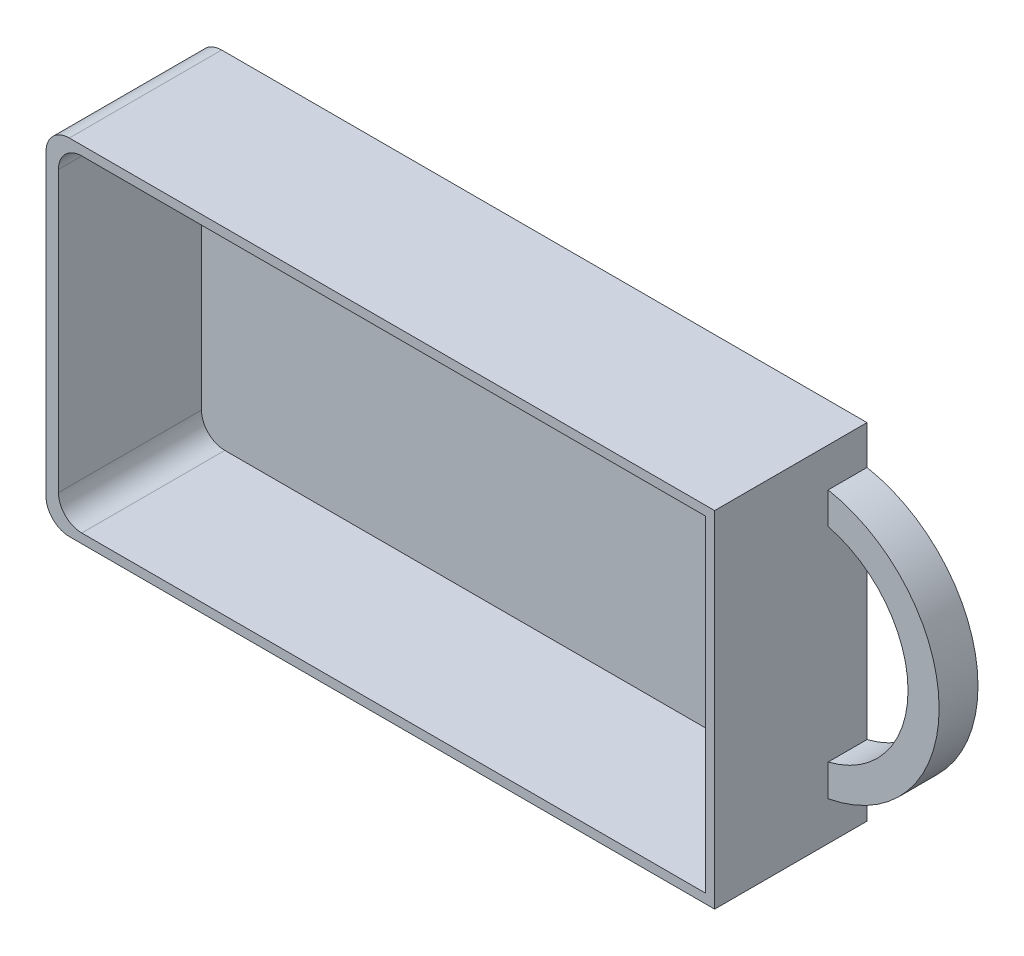
SolidWorks part; units mm, degrees
ref_plane "Спереди" through (0, 0, 0) normal (0, 0, 1) x (1, 0, 0)
ref_plane "Сверху" through (0, 0, 0) normal (0, 1, 0) x (1, 0, 0)
ref_plane "Справа" through (0, 0, 0) normal (1, 0, 0) x (0, 0, -1)
other "Configuration Table"
sketch "Эскиз1" plane through (0, 0, 0) normal (0, 0, 1) x (1, 0, 0)
  line L1 (-43, 22.2) -> (43, 22.2)
  line L2 (-43, 22.2) -> (-43, -22.2)
  line L3 (-43, -22.2) -> (43, -22.2)
  line L4 (43, 22.2) -> (43, -22.2)
  line L5 (-43, 22.2) -> (43, -22.2) construction
  line L6 (-43, -22.2) -> (43, 22.2) construction
  point P0 (0, 0)
  dimension "D1" = 86
  dimension "D2" = 44.4
extrude "Бобышка-Вытянуть1" add sketch "Эскиз1" along normal blind 19.6
sketch "Эскиз2" plane through (0, 0, 0) normal (0, 0, 1) x (1, 0, 0)
  line L0 (0, 0) -> (43, 0) construction
  line L1 (43, -22.2) -> (43, 22.2) construction
  line L2 (43, 17.2) -> (43, 13.1088)
  line L3 (43, -17.2) -> (43, -13.1088)
  arc A0 (43, -17.2) -> (43, 17.2) centre (39.7735, 0) ccw
  arc A1 (43, -13.1088) -> (43, 13.1088) centre (39.7735, 0) ccw
  dimension "D3" = 13.5
  dimension "D4" = 4
  dimension "D1" = 5
  dimension "D2" = 5
extrude "Бобышка-Вытянуть2" add sketch "Эскиз2" along normal blind 5
sketch "Эскиз3" plane through (0, 0, 19.6) normal (0, 0, 1) x (1, 0, 0)
  line L5 (-41.4, 22.2) -> (-41.4, -22.2)
  line L6 (-43, -21) -> (41.8, -21)
  line L7 (41.8, -21) -> (41.8, 21)
  line L8 (41.8, 21) -> (-43, 21)
  line L9 (-41.4, -21) -> (41.8, -21)
  line L10 (41.8, -21) -> (41.8, 21)
  line L11 (41.8, 21) -> (-41.4, 21)
  line L12 (-41.4, 21) -> (-41.4, -21)
  dimension "D1" = 1.2
  dimension "D2" = 1.6
extrude "Вырез-Вытянуть1" cut sketch "Эскиз3" against normal offset from surface (18.4 mm away) 1.2 up to face at (48.1368, 0, 0)
fillet "Скругление1" radius 3 4 edges at (-43, 22.2, 9.8) (-43, -22.2, 9.8) (-41.4, -21, 10.4) (-41.4, 21, 10.4)
